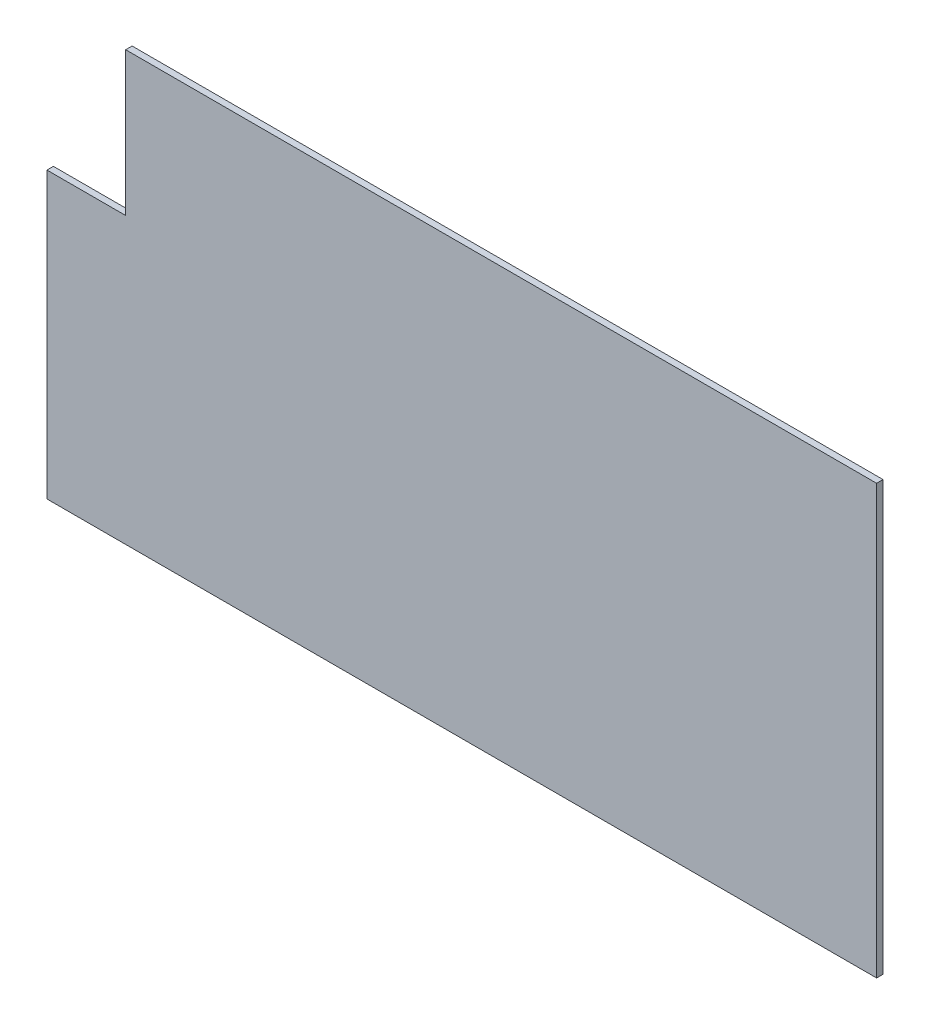
SolidWorks part; units mm, degrees
material "Acrylic (Medium-high impact)"
ref_plane "Front Plane" through (0, 0, 0) normal (0, 0, 1) x (1, 0, 0)
ref_plane "Top Plane" through (0, 0, 0) normal (0, 1, 0) x (1, 0, 0)
ref_plane "Right Plane" through (0, 0, 0) normal (1, 0, 0) x (0, 0, -1)
sketch "Sketch1" plane through (0, 0, 0) normal (0, 0, 1) x (1, 0, 0)
  line L1 (-289.5, -149.5) -> (289.5, -149.5)
  line L2 (-289.5, -149.5) -> (-289.5, 149.5)
  line L3 (-289.5, 149.5) -> (289.5, 149.5)
  line L4 (289.5, -149.5) -> (289.5, 149.5)
  line L5 (-289.5, -149.5) -> (289.5, 149.5) construction
  line L6 (-289.5, 149.5) -> (289.5, -149.5) construction
  point P0 (0, 0)
  dimension "D1" = 579
  dimension "D2" = 299
extrude "Boss-Extrude1" add sketch "Sketch1" along normal mid plane 4.4958
sketch "Sketch2" plane through (0, 0, -2.2479) normal (0, 0, -1) x (-1, 0, 0)
  line L0 (236.25, 50.3) -> (284.75, 50.3) construction
  line L1 (235.55, 50.3) -> (289.5, 50.3) construction
  line L2 (235.55, 51) -> (235.55, 149) construction
  line L3 (235.55, 50.3) -> (235.55, 149.5) construction
  line L4 (289.5, 49.3) -> (289.5, 149.5)
  line L5 (289.5, 149.5) -> (289.5, -149.5) construction
  line L6 (289.5, 149.5) -> (234.55, 149.5)
  line L7 (234.55, 49.3) -> (234.55, 149.5)
  line L10 (234.55, 49.3) -> (289.5, 49.3)
  line L11 (289.5, 50.3) -> (289.5, 149.5) construction
  line L12 (289.5, 149.5) -> (235.55, 149.5) construction
  line L13 (234.55, 49.3) -> (234.55, 150.5) construction
  line L14 (234.55, 49.3) -> (290.5, 49.3) construction
  line L15 (290.5, 49.3) -> (290.5, 150.5) construction
  line L16 (290.5, 150.5) -> (234.55, 150.5) construction
  dimension "D1" = 1
extrude "Cut-Extrude1" cut sketch "Sketch2" against normal up to surface (4.4958 mm away) up to face at (0, 0, 2.2479)
